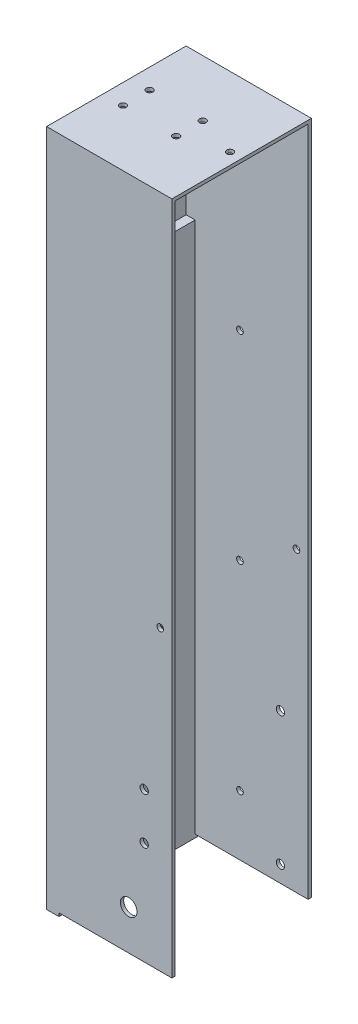
SolidWorks part; units mm, degrees
ref_plane "Alzado" through (0, 0, 0) normal (0, 0, 1) x (1, 0, 0)
ref_plane "Planta" through (0, 0, 0) normal (0, 1, 0) x (1, 0, 0)
ref_plane "Vista lateral" through (0, 0, 0) normal (1, 0, 0) x (0, 0, -1)
sketch "Sketch1" plane through (0, 0, 0) normal (1, 0, 0) x (0, 0, -1)
  line L1 (-13.831, 10.0882) -> (28.169, 10.0882)
  line L2 (-13.831, 10.0882) -> (-13.831, -159.9118)
  line L3 (-13.831, -159.9118) -> (28.169, -159.9118)
  line L4 (28.169, 10.0882) -> (28.169, -159.9118)
  dimension "D1" = 42
  dimension "D2" = 170
extrude "Boss-Extrude1" add sketch "Sketch1" along normal blind 1
sketch "Sketch2" plane through (1, 0, 0) normal (1, 0, 0) x (0, 0, -1)
  line L0 (28.169, 10.0882) -> (-13.831, 10.0882) construction
  line L1 (28.169, -159.9118) -> (27.169, -159.9118)
  line L2 (28.169, -159.9118) -> (28.169, 10.0882)
  line L3 (28.169, 10.0882) -> (27.169, 10.0882)
  line L4 (27.169, -159.9118) -> (27.169, 10.0882)
  line L6 (-13.831, -159.9118) -> (28.169, -159.9118) construction
  line L7 (-13.831, 10.0882) -> (-12.831, 10.0882)
  line L8 (-13.831, 10.0882) -> (-13.831, -159.9118)
  line L9 (-13.831, -159.9118) -> (-12.831, -159.9118)
  line L10 (-12.831, 10.0882) -> (-12.831, -159.9118)
  dimension "D1" = 1
  dimension "D2" = 1
extrude "Boss-Extrude2" add sketch "Sketch2" along normal blind 50
sketch "Sketch4" plane through (0, 10.0882, 0) normal (0, 1, 0) x (1, 0, 0)
  line L0 (51, 28.169) -> (51, 27.169)
  line L1 (51, 27.169) -> (1, 27.169)
  line L2 (1, 27.169) -> (1, -12.831)
  line L3 (1, -12.831) -> (51, -12.831)
  line L4 (51, -12.831) -> (51, -13.831)
  line L5 (51, -13.831) -> (0, -13.831)
  line L6 (0, -13.831) -> (0, 28.169)
  line L7 (0, 28.169) -> (51, 28.169)
extrude "Boss-Extrude3" add sketch "Sketch4" along normal blind 30
sketch "Sketch5" plane through (0, -159.9118, 0) normal (0, -1, 0) x (1, 0, 0)
  line L0 (1, 12.831) -> (10, 12.831) construction
  line L1 (51, 12.831) -> (1, 12.831) construction
  line L2 (51, 13.831) -> (0, 13.831) construction
  line L3 (10, 12.831) -> (11, 12.831)
  line L4 (10, 12.831) -> (10, 13.831)
  line L5 (10, 13.831) -> (11, 13.831)
  line L6 (11, 12.831) -> (11, 13.831)
  dimension "D1" = 9
  dimension "D2" = 1
extrude "Cut-Extrude1" cut sketch "Sketch5" against normal blind 170
sketch "Sketch6" plane through (0, -159.9118, 0) normal (0, -1, 0) x (1, 0, 0)
  line L0 (10, 12.831) -> (10, -27.169) construction
  line L1 (51, -27.169) -> (1, -27.169) construction
  line L2 (10, -27.169) -> (14, -27.169) construction
  line L3 (51, -28.169) -> (0, -28.169) construction
  line L4 (14, -27.169) -> (15, -27.169)
  line L5 (14, -27.169) -> (14, -28.169)
  line L6 (14, -28.169) -> (15, -28.169)
  line L7 (15, -27.169) -> (15, -28.169)
  dimension "D1" = 4
  dimension "D2" = 1
extrude "Cut-Extrude2" cut sketch "Sketch6" against normal blind 170
sketch "Sketch9" plane through (0, 0, 13.831) normal (0, 0, 1) x (1, 0, 0)
  line L0 (11, -159.9118) -> (26, -159.9118) construction
  line L1 (51, -159.9118) -> (11, -159.9118) construction
  line L2 (26, -159.9118) -> (26, -144.9118) construction
  circle A0 centre (26, -144.9118) radius 1.5
  dimension "D1" = 15
extrude "Cut-Extrude3" cut sketch "Sketch9" against normal blind 10
sketch "Sketch10" plane through (0, 0, 13.831) normal (0, 0, 1) x (1, 0, 0)
  line L0 (26, -144.9118) -> (11, -144.9118) construction
  line L1 (11, 10.0882) -> (11, -159.9118) construction
  line L2 (26, -159.9118) -> (26, -148.9118) construction
  line L3 (51, -159.9118) -> (11, -159.9118) construction
  circle A0 centre (26, -148.9118) radius 1.5
  dimension "D1" = 11
extrude "Cut-Extrude4" cut sketch "Sketch10" against normal blind 10
sketch "Sketch11" plane through (0, 0, 13.831) normal (0, 0, 1) x (1, 0, 0)
  circle A0 centre (26, -144.9118) radius 2.0283
extrude "Boss-Extrude4" add sketch "Sketch11" against normal blind 1
sketch "Sketch13" plane through (1, 0, 0) normal (1, 0, 0) x (0, 0, -1)
  line L0 (27.169, 40.0882) -> (27.169, 10.0882) construction
  line L1 (27.169, 40.0882) -> (27.169, -159.9118) construction
  line L3 (-12.831, 40.0882) -> (27.169, 40.0882)
  line L4 (-12.831, 40.0882) -> (-12.831, 17.1882)
  line L5 (-12.831, 17.1882) -> (27.169, 17.1882)
  line L6 (27.169, 40.0882) -> (27.169, 17.1882)
  dimension "D1" = 30
  dimension "D2" = 22.9
extrude "Boss-Extrude5" add sketch "Sketch13" along normal blind 50
sketch "Sketch14" plane through (51, 0, 0) normal (1, 0, 0) x (0, 0, -1)
  line L0 (28.169, -159.9118) -> (28.169, 40.0882) construction
  line L1 (-13.831, 40.0882) -> (28.169, 40.0882)
  line L2 (-13.831, 40.0882) -> (-13.831, 18.1882)
  line L3 (-13.831, 18.1882) -> (28.169, 18.1882)
  line L4 (28.169, 40.0882) -> (28.169, 18.1882)
  dimension "D1" = 21.9
extrude "Cut-Extrude6" cut sketch "Sketch14" against normal blind 60
sketch "Sketch17" plane through (0, 17.1882, 0) normal (0, -1, 0) x (1, 0, 0)
  line L0 (1, -7.169) -> (11.5, -7.169) construction
  line L1 (1, 12.831) -> (1, -27.169) construction
  line L2 (11.5, -7.169) -> (23.29, -7.169) construction
  circle A0 centre (23.29, -11.169) radius 1
  circle A1 centre (23.29, -3.169) radius 1
  circle A2 centre (7.29, -11.169) radius 1
  circle A3 centre (7.29, -3.169) radius 1
  dimension "D3" = 4
  dimension "D5" = 16
  dimension "D1" = 10.5
  dimension "D2" = 11.79
  dimension "D4" = 4
extrude "Cut-Extrude7" cut sketch "Sketch17" against normal blind 10
sketch "Sketch18" plane through (0, -159.9118, 0) normal (0, -1, 0) x (1, 0, 0)
  line L1 (51, 12.831) -> (11, 12.831)
  line L2 (51, 12.831) -> (51, 13.831)
  line L3 (51, 13.831) -> (11, 13.831)
  line L4 (11, 12.831) -> (11, 13.831)
  line L5 (51, -28.169) -> (15, -28.169)
  line L6 (51, -28.169) -> (51, -27.169)
  line L7 (51, -27.169) -> (15, -27.169)
  line L8 (15, -28.169) -> (15, -27.169)
  line L9 (14, -28.169) -> (1, -28.169)
  line L10 (14, -28.169) -> (14, -27.169)
  line L11 (14, -27.169) -> (1, -27.169)
  line L12 (1, -28.169) -> (1, -27.169)
  line L13 (10, 13.831) -> (1, 13.831)
  line L14 (10, 13.831) -> (10, 12.831)
  line L15 (10, 12.831) -> (1, 12.831)
  line L16 (1, 13.831) -> (1, 12.831)
extrude "Boss-Extrude7" add sketch "Sketch18" along normal blind 1
sketch "Sketch19" plane through (0, -159.9118, 0) normal (0, -1, 0) x (1, 0, 0)
  line L1 (0, -28.169) -> (1, -28.169)
  line L2 (0, -28.169) -> (0, 13.831)
  line L3 (0, 13.831) -> (1, 13.831)
  line L4 (1, -28.169) -> (1, 13.831)
extrude "Boss-Extrude8" add sketch "Sketch19" along normal blind 1
sketch "Sketch20" plane through (0, 0, -28.169) normal (0, 0, -1) x (-1, 0, 0)
  line L1 (-15, 10.0882) -> (-13.9999, 10.0882)
  line L2 (-15, 10.0882) -> (-15, 11.0882)
  line L3 (-15, 11.0882) -> (-13.9999, 11.0882)
  line L4 (-13.9999, 10.0882) -> (-13.9999, 11.0882)
  dimension "D1" = 1
extrude "Cut-Extrude8" cut sketch "Sketch20" against normal blind 1
sketch "Sketch21" plane through (0, 0, 13.831) normal (0, 0, 1) x (1, 0, 0)
  line L1 (10, 10.0882) -> (11, 10.0882)
  line L2 (10, 10.0882) -> (10, 11.0882)
  line L3 (10, 11.0882) -> (11, 11.0882)
  line L4 (11, 10.0882) -> (11, 11.0882)
  dimension "D1" = 1
extrude "Cut-Extrude9" cut sketch "Sketch21" against normal blind 1
sketch "Sketch22" plane through (0, 0, 13.831) normal (0, 0, 1) x (1, 0, 0)
  line L0 (51, -160.9118) -> (11, -160.9118) construction
  line L1 (38, -160.9118) -> (39, -160.9118)
  line L2 (38, -160.9118) -> (38, -129.9118)
  line L3 (38, -129.9118) -> (39, -129.9118)
  line L4 (39, -160.9118) -> (39, -129.9118)
  dimension "D1" = 1
  dimension "D2" = 31
extrude "Boss-Extrude9" add sketch "Sketch22" against normal through all
sketch "Sketch26" plane through (0, -160.9118, 0) normal (0, -1, 0) x (-1, 0, 0)
  line L0 (-15, 28.169) -> (-51, 28.169) construction
  line L1 (-27.8775, 28.169) -> (-16.3775, 28.169)
  line L2 (-27.8775, 28.169) -> (-27.8775, -13.831)
  line L3 (-27.8775, -13.831) -> (-16.3775, -13.831)
  line L4 (-16.3775, 28.169) -> (-16.3775, -13.831)
  line L5 (-51, -13.831) -> (-11, -13.831) construction
  dimension "D1" = 11.5
extrude "Boss-Extrude13" add sketch "Sketch26" along normal blind 1
sketch "Sketch35" plane through (39, 0, 0) normal (1, 0, 0) x (0, 0, -1)
  line L1 (27.169, -129.9118) -> (-12.831, -129.9118)
  line L2 (27.169, -129.9118) -> (27.169, -160.9118)
  line L3 (27.169, -160.9118) -> (-12.831, -160.9118)
  line L4 (-12.831, -129.9118) -> (-12.831, -160.9118)
extrude "Cut-Extrude17" cut sketch "Sketch35" against normal blind 27
sketch "Sketch36" plane through (27.8775, 0, 0) normal (1, 0, 0) x (0, 0, -1)
  line L1 (-13.831, -160.9118) -> (28.169, -160.9118)
  line L2 (-13.831, -160.9118) -> (-13.831, -161.9118)
  line L3 (-13.831, -161.9118) -> (28.169, -161.9118)
  line L4 (28.169, -160.9118) -> (28.169, -161.9118)
extrude "Cut-Extrude18" cut sketch "Sketch36" against normal blind 24
sketch "Sketch37" plane through (0, 0, 13.831) normal (0, 0, 1) x (1, 0, 0)
  line L1 (51, -160.9118) -> (39, -160.9118)
  line L2 (51, -160.9118) -> (51, 51.8324)
  line L3 (51, 51.8324) -> (39, 51.8324)
  line L4 (39, -160.9118) -> (39, 51.8324)
  dimension "D1" = 12
extrude "Cut-Extrude19" cut sketch "Sketch37" against normal blind 50
sketch "Sketch39" plane through (0, 0, -28.169) normal (0, 0, -1) x (-1, 0, 0)
  line L0 (-15, -155.9118) -> (-30.67, -155.9118) construction
  line L1 (-15, 11.0882) -> (-15, -160.9118) construction
  line L2 (-15, -160.9118) -> (-39, -160.9118) construction
  circle A0 centre (-30.67, -155.9118) radius 1.25
  dimension "D1" = 15.67
  dimension "D2" = 5
extrude "Cut-Extrude20" cut sketch "Sketch39" against normal blind 10
sketch "Sketch40" plane through (0, 0, -28.169) normal (0, 0, -1) x (-1, 0, 0)
  line L0 (-30.67, -155.9118) -> (-30.67, -129.9118) construction
  circle A0 centre (-30.67, -129.9118) radius 1.25
  dimension "D1" = 26
extrude "Cut-Extrude21" cut sketch "Sketch40" against normal blind 10
sketch "Sketch41" plane through (0, 0, -28.169) normal (0, 0, -1) x (-1, 0, 0)
  circle A0 centre (-30.67, -129.9118) radius 2.5908
extrude "Boss-Extrude14" add sketch "Sketch41" against normal blind 1
sketch "Sketch42" plane through (0, 0, -28.169) normal (0, 0, -1) x (-1, 0, 0)
  line L0 (-30.67, -155.9118) -> (-30.67, -115.9118) construction
  circle A0 centre (-30.67, -115.9118) radius 1.25
  dimension "D1" = 40
extrude "Cut-Extrude22" cut sketch "Sketch42" against normal blind 1
sketch "Sketch43" plane through (0, 0, 13.831) normal (0, 0, 1) x (1, 0, 0)
  line L0 (30.67, -128.9118) -> (30.67, -115.9118) construction
  line L2 (11, 11.0882) -> (11, -160.9118) construction
  circle A0 centre (30.67, -128.9118) radius 1.25
  circle A1 centre (30.67, -115.9118) radius 1.25
  dimension "D1" = 13
  dimension "D2" = 19.67
extrude "Cut-Extrude23" cut sketch "Sketch43" against normal blind 1
sketch "Sketch44" plane through (0, 0, 13.831) normal (0, 0, 1) x (1, 0, 0)
  circle A1 centre (27.1096, -127.2762) radius 6.3922
extrude "Boss-Extrude16" add sketch "Sketch44" against normal blind 1
sketch "Sketch45" plane through (0, 0, 13.831) normal (0, 0, 1) x (1, 0, 0)
  line L0 (30.67, -115.9118) -> (30.67, -129.9118) construction
  circle A0 centre (30.67, -129.9118) radius 1.25
  dimension "D1" = 14
extrude "Cut-Extrude24" cut sketch "Sketch45" against normal blind 1
sketch "Sketch46" plane through (0, 18.1882, 0) normal (0, 1, 0) x (1, 0, 0)
  line L0 (7.29, 11.169) -> (1.29, 11.169) construction
  line L1 (0, 28.169) -> (39, 28.169) construction
  line L2 (1.29, 28.169) -> (0, 28.169)
  line L3 (1.29, 28.169) -> (1.29, -13.831)
  line L4 (1.29, -13.831) -> (0, -13.831)
  line L5 (0, 28.169) -> (0, -13.831)
  dimension "D1" = 6
extrude "Cut-Extrude25" cut sketch "Sketch46" against normal blind 190
sketch "Sketch47" plane through (0, 18.1882, 0) normal (0, 1, 0) x (1, 0, 0)
  line L0 (1.29, -13.831) -> (39, -13.831) construction
  line L1 (1.29, 28.169) -> (2.29, 28.169)
  line L2 (1.29, 28.169) -> (1.29, -13.831)
  line L3 (1.29, -13.831) -> (2.29, -13.831)
  line L4 (2.29, 28.169) -> (2.29, -13.831)
  dimension "D1" = 1
extrude "Boss-Extrude17" add sketch "Sketch47" against normal blind 179.1
sketch "Sketch48" plane through (0, 0, -28.169) normal (0, 0, -1) x (-1, 0, 0)
  line L0 (-1.29, -160.9118) -> (-1.29, 18.1882) construction
  line L2 (-39, -160.9118) -> (-1.29, -160.9118)
  line L3 (-39, -160.9118) -> (-39, -160.8118)
  line L4 (-39, -160.8118) -> (-1.29, -160.8118)
  line L5 (-1.29, -160.9118) -> (-1.29, -160.8118)
  dimension "0.1" = 0.1
extrude "Cut-Extrude26" cut sketch "Sketch48" against normal blind 179.1
sketch "Sketch50" plane through (2.29, 0, 0) normal (1, 0, 0) x (0, 0, -1)
  line L0 (27.169, -160.8118) -> (-12.831, -160.8118) construction
  line L1 (12.169, -160.8118) -> (2.169, -160.8118)
  line L2 (12.169, -160.8118) -> (12.169, -40.8118)
  line L3 (12.169, -40.8118) -> (2.169, -40.8118)
  line L4 (2.169, -160.8118) -> (2.169, -40.8118)
  dimension "D1" = 10
  dimension "D2" = 15
  dimension "D3" = 120
extrude "Boss-Extrude20" add sketch "Sketch50" along normal blind 4
sketch "Sketch52" plane through (0, -160.8118, 0) normal (0, -1, 0) x (1, 0, 0)
  line L1 (39, 13.831) -> (11, 13.831)
  line L2 (39, 13.831) -> (39, 12.831)
  line L3 (39, 12.831) -> (11, 12.831)
  line L4 (11, 13.831) -> (11, 12.831)
  line L5 (39, -27.169) -> (15, -27.169)
  line L6 (39, -27.169) -> (39, -28.169)
  line L7 (39, -28.169) -> (15, -28.169)
  line L8 (15, -27.169) -> (15, -28.169)
extrude "Boss-Extrude21" add sketch "Sketch52" along normal blind 0.1
sketch "Sketch53" plane through (0, -160.8118, 0) normal (0, -1, 0) x (-1, 0, 0)
  line L0 (-10, -13.831) -> (-10, -12.831)
  line L1 (-10, -12.831) -> (-2.29, -12.831)
  line L2 (-2.29, -12.831) -> (-2.29, 2.169)
  line L3 (-2.29, 2.169) -> (-6.29, 2.169)
  line L4 (-6.29, 2.169) -> (-6.29, 12.169) construction
  line L5 (-6.29, 2.169) -> (-6.29, 12.169)
  line L6 (-6.29, 12.169) -> (-2.29, 12.169)
  line L7 (-2.29, 12.169) -> (-2.29, 27.169)
  line L8 (-2.29, 27.169) -> (-13.9999, 27.169)
  line L9 (-13.9999, 27.169) -> (-14, 28.169)
  line L10 (-14, 28.169) -> (-1.29, 28.169)
  line L11 (-1.29, 28.169) -> (-1.29, -13.831)
  line L12 (-1.29, -13.831) -> (-10, -13.831)
extrude "Boss-Extrude22" add sketch "Sketch53" along normal blind 0.1
sketch "Sketch54" plane through (6.29, 0, 0) normal (1, 0, 0) x (0, 0, -1)
  line L1 (2.169, -40.8118) -> (12.169, -40.8118)
  line L2 (2.169, -40.8118) -> (2.169, -160.9118)
  line L3 (2.169, -160.9118) -> (12.169, -160.9118)
  line L4 (12.169, -40.8118) -> (12.169, -160.9118)
extrude "Boss-Extrude23" add sketch "Sketch54" along normal blind 3.71
sketch "Sketch55" plane through (0, -160.9118, 0) normal (0, -1, 0) x (1, 0, 0)
  line L0 (1.29, -28.169) -> (14, -28.169) construction
  line L1 (1.29, 13.831) -> (5.49, 13.831)
  line L2 (1.29, 13.831) -> (1.29, -28.169)
  line L3 (1.29, -28.169) -> (5.49, -28.169)
  line L4 (5.49, 13.831) -> (5.49, -28.169)
  dimension "D1" = 4.2
extrude "Boss-Extrude24" add sketch "Sketch55" along normal blind 1
sketch "Sketch56" plane through (0, -161.9118, 0) normal (0, -1, 0) x (1, 0, 0)
  line L0 (1.29, -28.169) -> (5.49, -28.169) construction
  line L1 (5.49, 13.831) -> (5, 13.831)
  line L2 (5.49, 13.831) -> (5.49, -28.169)
  line L3 (5.49, -28.169) -> (5, -28.169)
  line L4 (5, 13.831) -> (5, -28.169)
  dimension "D1" = 0.49
extrude "Cut-Extrude27" cut sketch "Sketch56" against normal blind 1
sketch "Sketch58" plane through (0, 0, -28.169) normal (0, 0, -1) x (-1, 0, 0)
  line L0 (-17.5, 18.1882) -> (-17.5, -22.8118) construction
  line L1 (-1.29, 18.1882) -> (-39, 18.1882) construction
  line L2 (-15, 11.0882) -> (-15, -160.9118) construction
  circle A0 centre (-17.5, -22.8118) radius 1
  dimension "D1" = 41
  dimension "D2" = 2.5
extrude "Cut-Extrude28" cut sketch "Sketch58" against normal blind 1
sketch "Sketch59" plane through (0, 0, -28.169) normal (0, 0, -1) x (-1, 0, 0)
  circle A0 centre (-17.5, -22.8118) radius 1.8688
extrude "Boss-Extrude25" add sketch "Sketch59" against normal blind 1
sketch "Sketch60" plane through (0, 0, -28.169) normal (0, 0, -1) x (-1, 0, 0)
  line L0 (-18.5, 18.1882) -> (-18.5, -22.8118) construction
  line L2 (-1.29, 18.1882) -> (-39, 18.1882) construction
  line L3 (-15, 11.0882) -> (-15, -160.9118) construction
  circle A0 centre (-18.5, -22.8118) radius 1
  dimension "D1" = 41
  dimension "D2" = 3.5
extrude "Cut-Extrude29" cut sketch "Sketch60" against normal blind 1
sketch "Sketch61" plane through (0, 0, -28.169) normal (0, 0, -1) x (-1, 0, 0)
  line L0 (-18.5, -22.8118) -> (-18.5, -82.8118) construction
  circle A0 centre (-18.5, -82.8118) radius 1
  dimension "D1" = 60
extrude "Cut-Extrude30" cut sketch "Sketch61" against normal blind 1
sketch "Sketch62" plane through (0, 0, -28.169) normal (0, 0, -1) x (-1, 0, 0)
  line L1 (-16.4269, 11.7305) -> (-11, 11.7305)
  line L2 (-16.4269, 11.7305) -> (-16.4269, -160.9118)
  line L3 (-16.4269, -160.9118) -> (-11, -160.9118)
  line L4 (-11, 11.7305) -> (-11, -160.9118)
extrude "Boss-Extrude26" add sketch "Sketch62" against normal blind 1
sketch "Sketch63" plane through (0, 0, 13.831) normal (0, 0, 1) x (1, 0, 0)
  line L0 (10, -160.9118) -> (5, -160.9118) construction
  line L1 (14.3683, 14.6634) -> (8.794, 14.6634)
  line L2 (14.3683, 14.6634) -> (14.3683, -160.9118)
  line L3 (14.3683, -160.9118) -> (8.794, -160.9118)
  line L4 (8.794, 14.6634) -> (8.794, -160.9118)
extrude "Boss-Extrude27" add sketch "Sketch63" against normal blind 1
sketch "Sketch64" plane through (0, -161.9118, 0) normal (0, -1, 0) x (1, 0, 0)
  line L1 (5, 13.831) -> (1.29, 13.831)
  line L2 (5, 13.831) -> (5, -28.169)
  line L3 (5, -28.169) -> (1.29, -28.169)
  line L4 (1.29, 13.831) -> (1.29, -28.169)
extrude "Boss-Extrude29" add sketch "Sketch64" against normal blind 121.1
sketch "Sketch66" plane through (0, 0, -28.169) normal (0, 0, -1) x (-1, 0, 0)
  line L0 (-39, 18.1882) -> (-39, -71.3618) construction
  line L1 (-39, 18.1882) -> (-39, -160.9118) construction
  line L2 (-39, -71.3618) -> (-35.5, -71.3618) construction
  circle A0 centre (-35.5, -71.3618) radius 1
  dimension "D1" = 3.5
extrude "Cut-Extrude31" cut sketch "Sketch66" against normal through all
sketch "Sketch67" plane through (0, 18.1882, 0) normal (0, 1, 0) x (1, 0, 0)
  line L0 (39, -13.831) -> (39, 28.169) construction
  line L1 (1.29, 28.169) -> (39, 28.169) construction
  circle A0 centre (35.5, 7.169) radius 1
  dimension "D1" = 3.5
  dimension "D2" = 21
extrude "Cut-Extrude32" cut sketch "Sketch67" against normal blind 1
sketch "Sketch68" plane through (0, 0, 13.831) normal (0, 0, 1) x (1, 0, 0)
  circle A0 centre (26, -148.9118) radius 2.5
extrude "Cut-Extrude33" cut sketch "Sketch68" against normal blind 10
sketch "Sketch71" plane through (0, 0, -28.169) normal (0, 0, -1) x (-1, 0, 0)
  line L0 (-18.5, -82.8118) -> (-18.5, -142.8118) construction
  circle A0 centre (-18.5, -142.8118) radius 1
  dimension "D1" = 60
extrude "Cut-Extrude35" cut sketch "Sketch71" against normal blind 10
sketch "Sketch72" plane through (0, 0, -28.169) normal (0, 0, -1) x (-1, 0, 0)
  line L1 (-39, 18.1882) -> (-1.29, 18.1882)
  line L2 (-39, 18.1882) -> (-39, 38.1882)
  line L3 (-39, 38.1882) -> (-1.29, 38.1882)
  line L4 (-1.29, 18.1882) -> (-1.29, 38.1882)
  dimension "D1" = 20
extrude "Boss-Extrude30" add sketch "Sketch72" against normal blind 42
sketch "Sketch73" plane through (0, 17.1882, 0) normal (0, -1, 0) x (1, 0, 0)
  circle A0 centre (7.29, -3.169) radius 1
  circle A1 centre (23.29, -3.169) radius 1
  circle A2 centre (35.5, -7.169) radius 1
  circle A3 centre (23.29, -11.169) radius 1
  circle A4 centre (7.29, -11.169) radius 1
extrude "Cut-Extrude36" cut sketch "Sketch73" against normal blind 42
sketch "Sketch74" plane through (39, 0, 0) normal (1, 0, 0) x (0, 0, -1)
  line L0 (-13.831, 38.1882) -> (28.169, 38.1882) construction
  line L1 (-12.831, 17.1882) -> (27.169, 17.1882)
  line L2 (-12.831, 17.1882) -> (-12.831, 37.1882)
  line L3 (-12.831, 37.1882) -> (27.169, 37.1882)
  line L4 (27.169, 17.1882) -> (27.169, 37.1882)
  dimension "D1" = 1
extrude "Cut-Extrude38" cut sketch "Sketch74" against normal blind 36.71
sketch "Sketch75" plane through (0, 0, -28.169) normal (0, 0, -1) x (-1, 0, 0)
  line L1 (-39, 38.1882) -> (-1.29, 38.1882)
  line L2 (-39, 38.1882) -> (-39, 42.1882)
  line L3 (-39, 42.1882) -> (-1.29, 42.1882)
  line L4 (-1.29, 38.1882) -> (-1.29, 42.1882)
  dimension "D1" = 4
extrude "Boss-Extrude31" add sketch "Sketch75" against normal blind 42
sketch "Sketch76" plane through (0, 37.1882, 0) normal (0, -1, 0) x (1, 0, 0)
  circle A0 centre (35.5, -7.169) radius 1
  circle A1 centre (23.29, -3.169) radius 1
  circle A2 centre (23.29, -11.169) radius 1
  circle A3 centre (7.29, -3.169) radius 1
  circle A4 centre (7.29, -11.169) radius 1
extrude "Cut-Extrude39" cut sketch "Sketch76" against normal blind 42
sketch "Sketch77" plane through (39, 0, 0) normal (1, 0, 0) x (0, 0, -1)
  line L0 (-13.831, 42.1882) -> (28.169, 42.1882) construction
  line L1 (-12.831, 37.1882) -> (27.169, 37.1882)
  line L2 (-12.831, 37.1882) -> (-12.831, 41.1882)
  line L3 (-12.831, 41.1882) -> (27.169, 41.1882)
  line L4 (27.169, 37.1882) -> (27.169, 41.1882)
  dimension "D1" = 1
extrude "Cut-Extrude40" cut sketch "Sketch77" against normal blind 36.71
sketch "Sketch78" plane through (0, -40.8118, 0) normal (0, 1, 0) x (1, 0, 0)
  line L0 (10, 2.169) -> (5, 2.169)
  line L1 (5, 2.169) -> (5, -12.831)
  line L2 (5, -12.831) -> (2.29, -12.831)
  line L3 (2.29, -12.831) -> (2.29, 27.169)
  line L4 (2.29, 27.169) -> (2.29, -12.831) construction
  line L5 (2.29, 27.169) -> (5, 27.169)
  line L6 (5, 27.169) -> (5, 12.169)
  line L7 (5, 12.169) -> (10, 12.169)
  line L8 (10, 12.169) -> (10, 2.169)
extrude "Boss-Extrude32" add sketch "Sketch78" along normal blind 40
sketch "Sketch79" plane through (10, 0, 0) normal (1, 0, 0) x (0, 0, -1)
  line L0 (27.169, -0.8118) -> (-12.831, -0.8118) construction
  line L1 (8.3237, -17.8118) -> (9.4784, -15.8118)
  line L2 (9.4784, -15.8118) -> (8.3237, -13.8118)
  line L3 (8.3237, -13.8118) -> (6.0143, -13.8118)
  line L4 (6.0143, -13.8118) -> (4.8596, -15.8118)
  line L5 (4.8596, -15.8118) -> (6.0143, -17.8118)
  line L6 (6.0143, -17.8118) -> (8.3237, -17.8118)
  line L8 (12.169, -160.9118) -> (12.169, -0.8118) construction
  circle A0 centre (7.169, -15.8118) radius 2 construction
  dimension "D1" = 15
  dimension "D2" = 5
extrude "Cut-Extrude41" cut sketch "Sketch79" against normal blind 5
sketch "Sketch80" plane through (10, 0, 0) normal (1, 0, 0) x (0, 0, -1)
  line L1 (8.3237, -142.0411) -> (9.4784, -140.0411)
  line L2 (9.4784, -140.0411) -> (8.3237, -138.0411)
  line L3 (8.3237, -138.0411) -> (6.0143, -138.0411)
  line L4 (6.0143, -138.0411) -> (4.8596, -140.0411)
  line L5 (4.8596, -140.0411) -> (6.0143, -142.0411)
  line L6 (6.0143, -142.0411) -> (8.3237, -142.0411)
  circle A0 centre (7.169, -140.0411) radius 2 construction
extrude "Cut-Extrude42" cut sketch "Sketch80" against normal blind 5
sketch "Sketch81" plane through (10, 0, 0) normal (1, 0, 0) x (0, 0, -1)
  circle A1 centre (7.169, -15.8118) radius 1
extrude "Cut-Extrude43" cut sketch "Sketch81" against normal through all
sketch "Sketch82" plane through (10, 0, 0) normal (1, 0, 0) x (0, 0, -1)
  circle A1 centre (7.169, -140.0411) radius 1
extrude "Cut-Extrude44" cut sketch "Sketch82" against normal through all
